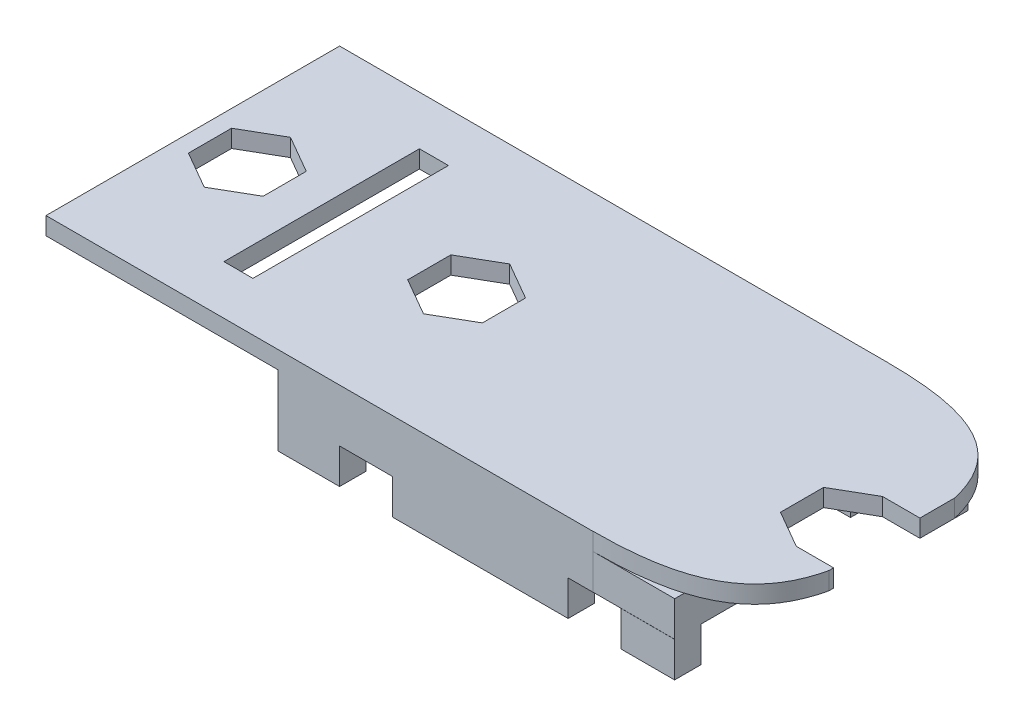
SolidWorks part; units mm, degrees
ref_plane "Front Plane" through (0, 0, 0) normal (0, 0, 1) x (1, 0, 0)
ref_plane "Top Plane" through (0, 0, 0) normal (0, 1, 0) x (1, 0, 0)
ref_plane "Right Plane" through (0, 0, 0) normal (1, 0, 0) x (0, 0, -1)
sketch "Sketch1" plane through (0, 0, 0) normal (0, 1, 0) x (1, 0, 0)
  line L1 (-40.0407, 20.9565) -> (-17.4855, 20.9565)
  line L2 (-40.0407, 20.9565) -> (-40.0407, 8.2565)
  line L3 (-40.0407, 8.2565) -> (-17.4855, 8.2565)
  line L4 (-17.4855, 20.9565) -> (-17.4855, 8.2565)
  dimension "D1" = 22.5552
  dimension "D2" = 12.7
extrude "Boss-Extrude1" add sketch "Sketch1" along normal blind 1
sketch "Sketch2" plane through (0, 1, 0) normal (0, 1, 0) x (1, 0, 0)
  line L0 (-17.4855, 20.9565) -> (-40.0407, 20.9565) construction
  line L1 (-40.0407, 18.2565) -> (-35.0407, 18.2565)
  line L2 (-40.0407, 18.2565) -> (-40.0407, 10.9565)
  line L3 (-40.0407, 10.9565) -> (-35.0407, 10.9565)
  line L4 (-35.0407, 18.2565) -> (-35.0407, 10.9565)
  line L7 (-40.0407, 20.9565) -> (-40.0407, 8.2565) construction
  dimension "D1" = 7.3
  dimension "D2" = 5
  dimension "D3" = 2.7
  dimension "D4" = 0
extrude "Cut-Extrude1" cut sketch "Sketch2" against normal blind 1
sketch "Sketch3" plane through (0, 1, 0) normal (0, 1, 0) x (1, 0, 0)
  line L0 (-17.4855, 8.2565) -> (-17.4855, 20.9565) construction
  line L1 (-17.4855, 16.2565) -> (-22.4855, 16.2565)
  line L2 (-17.4855, 16.2565) -> (-17.4855, 11.2565)
  line L3 (-17.4855, 11.2565) -> (-22.4855, 11.2565)
  line L4 (-22.4855, 16.2565) -> (-22.4855, 11.2565)
  line L5 (-40.0407, 8.2565) -> (-17.4855, 8.2565) construction
  line L6 (-17.4855, 20.9565) -> (-40.0407, 20.9565) construction
  dimension "D1" = 5
  dimension "D2" = 3
  dimension "D3" = 4.7
  dimension "D4" = 5
extrude "Cut-Extrude2" cut sketch "Sketch3" against normal blind 1
sketch "Sketch4" plane through (0, 0, 0) normal (0, -1, 0) x (1, 0, 0)
  line L0 (-17.4855, -8.2565) -> (-17.4855, -11.2565) construction
  line L1 (-40.0407, -8.2565) -> (-17.4855, -8.2565)
  line L2 (-40.0407, -8.2565) -> (-40.0407, -8.7565)
  line L3 (-40.0407, -8.7565) -> (-17.4855, -8.7565)
  line L4 (-17.4855, -8.2565) -> (-17.4855, -8.7565)
  line L5 (-40.0407, -20.9565) -> (-40.0407, -18.2565) construction
  line L6 (-17.4855, -8.2565) -> (-17.9855, -8.2565)
  line L7 (-17.4855, -8.2565) -> (-17.4855, -10.2565)
  line L8 (-17.4855, -10.2565) -> (-17.9855, -10.2565)
  line L9 (-17.9855, -8.2565) -> (-17.9855, -10.2565)
  line L10 (-40.0407, -20.4565) -> (-17.4855, -20.4565)
  line L11 (-40.0407, -20.4565) -> (-40.0407, -20.9565)
  line L12 (-40.0407, -20.9565) -> (-17.4855, -20.9565)
  line L13 (-17.4855, -20.4565) -> (-17.4855, -20.9565)
  line L15 (-17.4855, -20.9565) -> (-17.9855, -20.9565)
  line L16 (-17.4855, -20.9565) -> (-17.4855, -18.4565)
  line L17 (-17.4855, -18.4565) -> (-17.9855, -18.4565)
  line L18 (-17.9855, -20.9565) -> (-17.9855, -18.4565)
  line M3 (-17.4855, -11.2565) -> (-17.4855, -8.2565)
  line M5 (-40.0407, -8.2565) -> (-40.0407, -10.9565)
  line M9 (-40.0407, -18.2565) -> (-40.0407, -20.9565)
  line M10 (-40.0407, -20.9565) -> (-17.4855, -20.9565)
  line M11 (-17.4855, -20.9565) -> (-17.4855, -16.2565)
  dimension "D1" = 0.5
  dimension "D2" = 0.5
  dimension "D3" = 2
  dimension "D4" = 0.5
  dimension "D5" = 2.5
extrude "Boss-Extrude2" add sketch "Sketch4" along normal blind 1 contours L9 L1 L3 M5 | L3 L9 L8 M3 | L18 L10 L17 M11 | L18 L12 L10 M11 | L18 L10 M10 M9
sketch "Sketch5" plane through (0, 1, 0) normal (0, 1, 0) x (1, 0, 0)
  line L0 (-40.0407, 20.9565) -> (-40.0407, 18.2565) construction
  line L1 (-53.2407, 22.9565) -> (-13.4855, 22.9565)
  line L2 (-53.2407, 22.9565) -> (-53.2407, 6.2565)
  line L3 (-53.2407, 6.2565) -> (-13.4855, 6.2565)
  line L4 (-13.4855, 22.9565) -> (-13.4855, 6.2565)
  line L5 (-17.4855, 20.9565) -> (-40.0407, 20.9565) construction
  line L6 (-40.0407, 8.2565) -> (-17.4855, 8.2565) construction
  line L7 (-17.4855, 16.2565) -> (-17.4855, 20.9565) construction
  dimension "D1" = 13.2
  dimension "D2" = 2
  dimension "D3" = 2
  dimension "D4" = 4
extrude "Boss-Extrude3" add sketch "Sketch5" along normal blind 1
sketch "Sketch6" plane through (0, 2, 0) normal (0, 1, 0) x (1, 0, 0)
  line L0 (-35.0407, 10.9565) -> (-35.0407, 18.2565) construction
  line L1 (-39.7907, 13.3797) -> (-37.6657, 12.1528)
  line L2 (-37.6657, 12.1528) -> (-35.5407, 13.3797)
  line L3 (-35.5407, 13.3797) -> (-35.5407, 15.8334)
  line L4 (-35.5407, 15.8334) -> (-37.6657, 17.0603)
  line L5 (-37.6657, 17.0603) -> (-39.7907, 15.8334)
  line L6 (-39.7907, 15.8334) -> (-39.7907, 13.3797)
  line L8 (-53.2407, 6.2565) -> (-13.4855, 6.2565) construction
  circle A0 centre (-37.6657, 14.6065) radius 2.125 construction
  dimension "D1" = 4.25
  dimension "D2" = 0.5
  dimension "D3" = 8.35
extrude "Cut-Extrude3" cut sketch "Sketch6" against normal blind 1
sketch "Sketch7" plane through (0, 1, 0) normal (0, -1, 0) x (-1, 0, 0)
  line L0 (13.4855, 6.2565) -> (13.4855, 22.9565) construction
  line L1 (17.7355, 14.9834) -> (15.6105, 16.2103)
  line L2 (15.6105, 16.2103) -> (13.4855, 14.9834)
  line L3 (13.4855, 14.9834) -> (13.4855, 12.5297)
  line L4 (13.4855, 12.5297) -> (15.6105, 11.3028)
  line L5 (15.6105, 11.3028) -> (17.7355, 12.5297)
  line L6 (17.7355, 12.5297) -> (17.7355, 14.9834)
  circle A0 centre (15.6105, 13.7565) radius 2.125 construction
  dimension "D1" = 4.25
  dimension "D2" = 0
extrude "Cut-Extrude4" cut sketch "Sketch7" against normal blind 1
sketch "Sketch8" plane through (0, 2, 0) normal (0, 1, 0) x (1, 0, 0)
  line L0 (-13.4855, 22.9565) -> (-53.2407, 22.9565) construction
  line L1 (-13.4855, 14.9834) -> (-13.4855, 22.9565) construction
  spline S0 degree 3 poles (-22.1278, 22.9565) (-17.368, 22.9565) (-14.3027, 21.872) (-13.4855, 18.1762) knots 0 0 0 0 1 1 1 1
extrude "Cut-Extrude5" cut sketch "Sketch8" along direction (0, 1, 0) on the side against the normal through all and the other way through all
sketch "Sketch9" plane through (0, 2, 0) normal (0, 1, 0) x (1, 0, 0)
  line L0 (-22.1278, 22.9565) -> (-53.2407, 22.9565) construction
  line L1 (-53.2407, 6.2565) -> (-13.4855, 6.2565) construction
  point P0 (-32.2929, 14.6065)
  dimension "D1" = 8.35
  dimension "D2" = 8.35
ref_plane "Plane1" through (0, 0, -14.61) normal (0, 0, 1) x (1, 0, 0)
mirror "Mirror2" about plane through (0, 0, -14.61) normal (0, 0, 1) of "Cut-Extrude5"
sketch "Sketch10" plane through (0, 1, 0) normal (0, -1, 0) x (-1, 0, 0)
  line L0 (40.0407, 8.2565) -> (17.4855, 8.2565) construction
  line L1 (40.0407, 6.2565) -> (17.4855, 6.2565)
  line L2 (40.0407, 6.2565) -> (40.0407, 8.2565)
  line L3 (40.0407, 8.2565) -> (17.4855, 8.2565)
  line L4 (17.4855, 6.2565) -> (17.4855, 8.2565)
  line L5 (40.0407, 20.9565) -> (17.4855, 20.9565) construction
  line L6 (40.0407, 22.9565) -> (17.4855, 22.9565)
  line L7 (40.0407, 22.9565) -> (40.0407, 20.9565)
  line L8 (40.0407, 20.9565) -> (17.4855, 20.9565)
  line L9 (17.4855, 22.9565) -> (17.4855, 20.9565)
  line L10 (17.4855, 8.2565) -> (17.4855, 11.2565) construction
  line L11 (17.4855, 16.2565) -> (17.4855, 20.9565) construction
  dimension "D1" = 0
  dimension "D2" = 0
extrude "Boss-Extrude4" add sketch "Sketch10" along normal blind 2
sketch "Sketch11" plane through (0, 2, 0) normal (0, 1, 0) x (1, 0, 0)
  line L1 (-22.1278, 6.2635) -> (-13.2079, 6.2635)
  line L2 (-22.1278, 6.2635) -> (-22.1278, 5.533)
  line L3 (-22.1278, 5.533) -> (-13.2079, 5.533)
  line L4 (-13.2079, 6.2635) -> (-13.2079, 5.533)
extrude "Cut-Extrude6" cut sketch "Sketch11" against normal blind 3
sketch "Sketch12" plane through (0, -1, 0) normal (0, -1, 0) x (-1, 0, 0)
  line L0 (17.4855, 10.2565) -> (17.4855, 6.2635) construction
  line L1 (40.0407, 6.2565) -> (17.4855, 6.2565)
  line L2 (40.0407, 6.2565) -> (40.0407, 7.7565)
  line L3 (40.0407, 7.7565) -> (17.4855, 7.7565)
  line L4 (17.4855, 6.2565) -> (17.4855, 7.7565)
  line L5 (17.4855, 22.4089) -> (17.4855, 16.2565) construction
  line L6 (40.0407, 22.9565) -> (17.4855, 22.9565)
  line L7 (40.0407, 22.9565) -> (40.0407, 21.4565)
  line L8 (40.0407, 21.4565) -> (17.4855, 21.4565)
  line L9 (17.4855, 22.9565) -> (17.4855, 21.4565)
  dimension "D1" = 1.5
  dimension "D2" = 1.5
extrude "Boss-Extrude5" add sketch "Sketch12" along normal blind 2
sketch "Sketch13" plane through (0, -3, 0) normal (0, -1, 0) x (-1, 0, 0)
  line L0 (17.4855, 6.2565) -> (40.0407, 6.2565) construction
  line L1 (36.5407, 6.2565) -> (33.5407, 6.2565)
  line L2 (36.5407, 6.2565) -> (36.5407, 7.7565)
  line L3 (36.5407, 7.7565) -> (33.5407, 7.7565)
  line L4 (33.5407, 6.2565) -> (33.5407, 7.7565)
  line L5 (40.0407, 7.7565) -> (17.4855, 7.7565) construction
  line L6 (17.4855, 21.4565) -> (40.0407, 21.4565) construction
  line L7 (36.5407, 21.4565) -> (33.5407, 21.4565)
  line L8 (36.5407, 21.4565) -> (36.5407, 22.9565)
  line L9 (36.5407, 22.9565) -> (33.5407, 22.9565)
  line L10 (33.5407, 21.4565) -> (33.5407, 22.9565)
  line L11 (40.0407, 22.9565) -> (17.4855, 22.9565) construction
  line L12 (40.0407, 6.2565) -> (40.0407, 7.7565) construction
  line L13 (23.5407, 6.2565) -> (23.5407, 7.7565)
  line L14 (23.5407, 6.2565) -> (20.5407, 6.2565)
  line L15 (20.5407, 6.2565) -> (20.5407, 7.7565)
  line L16 (23.5407, 7.7565) -> (20.5407, 7.7565)
  line L17 (23.5407, 21.4565) -> (23.5407, 22.9565)
  line L18 (23.5407, 21.4565) -> (20.5407, 21.4565)
  line L19 (20.5407, 21.4565) -> (20.5407, 22.9565)
  line L20 (23.5407, 22.9565) -> (20.5407, 22.9565)
  line L21 (17.4855, 7.7565) -> (17.4855, 6.2565) construction
  dimension "D1" = 3
  dimension "D2" = 3.5
  dimension "D3" = 0
  dimension "D4" = 3
  dimension "D6" = 3.0552
  dimension "D5" = 2
extrude "Cut-Extrude7" cut sketch "Sketch13" against normal blind 2
sketch "Sketch14" plane through (0, 2, 0) normal (0, 1, 0) x (1, 0, 0)
  line L1 (-15.6105, 16.2103) -> (-13.4855, 16.2103)
  line L2 (-15.6105, 16.2103) -> (-15.6105, 14.9834)
  line L3 (-15.6105, 14.9834) -> (-13.4855, 14.9834)
  line L4 (-13.4855, 16.2103) -> (-13.4855, 14.9834)
  line L5 (-15.6105, 11.3028) -> (-13.4855, 11.3028)
  line L6 (-15.6105, 11.3028) -> (-15.6105, 12.5297)
  line L7 (-15.6105, 12.5297) -> (-13.4855, 12.5297)
  line L8 (-13.4855, 11.3028) -> (-13.4855, 12.5297)
extrude "Cut-Extrude8" cut sketch "Sketch14" against normal blind 1
sketch "Sketch15" plane through (0, 1, 0) normal (0, -1, 0) x (-1, 0, 0)
  line L0 (53.2407, 6.2565) -> (40.0407, 6.2565) construction
  line L1 (44.2607, 20.1665) -> (45.9107, 20.1665)
  line L2 (44.2607, 20.1665) -> (44.2607, 9.0465)
  line L3 (44.2607, 9.0465) -> (45.9107, 9.0465)
  line L4 (45.9107, 20.1665) -> (45.9107, 9.0465)
  line L5 (40.0407, 22.9565) -> (53.2407, 22.9565) construction
  line L6 (40.0407, 10.9565) -> (40.0407, 6.2565) construction
  line L8 (53.2407, 22.9565) -> (53.2407, 6.2565) construction
  dimension "D1" = 11.12
  dimension "D2" = 1.65
  dimension "D3" = 2.79
  dimension "D4" = 2.79
  dimension "D5" = 4.22
  dimension "D6" = 7.33
extrude "adapter_PCB_hole" cut sketch "Sketch15" against normal blind 1
sketch "Sketch22" plane through (0, 1, 0) normal (0, -1, 0) x (-1, 0, 0)
  line L0 (-2.75, 14.61) -> (2.75, 14.61) construction
  line L1 (52.2657, 15.8369) -> (50.1407, 17.0637)
  line L2 (50.1407, 17.0637) -> (48.0157, 15.8369)
  line L3 (48.0157, 15.8369) -> (48.0157, 13.3831)
  line L4 (48.0157, 13.3831) -> (50.1407, 12.1563)
  line L5 (50.1407, 12.1563) -> (52.2657, 13.3831)
  line L6 (52.2657, 13.3831) -> (52.2657, 15.8369)
  line L7 (53.2407, 22.9565) -> (53.2407, 6.2565) construction
  circle A0 centre (50.1407, 14.61) radius 2.125 construction
  dimension "D1" = 3.1
extrude "Cut-Extrude10" cut sketch "Sketch22" against normal blind 1
